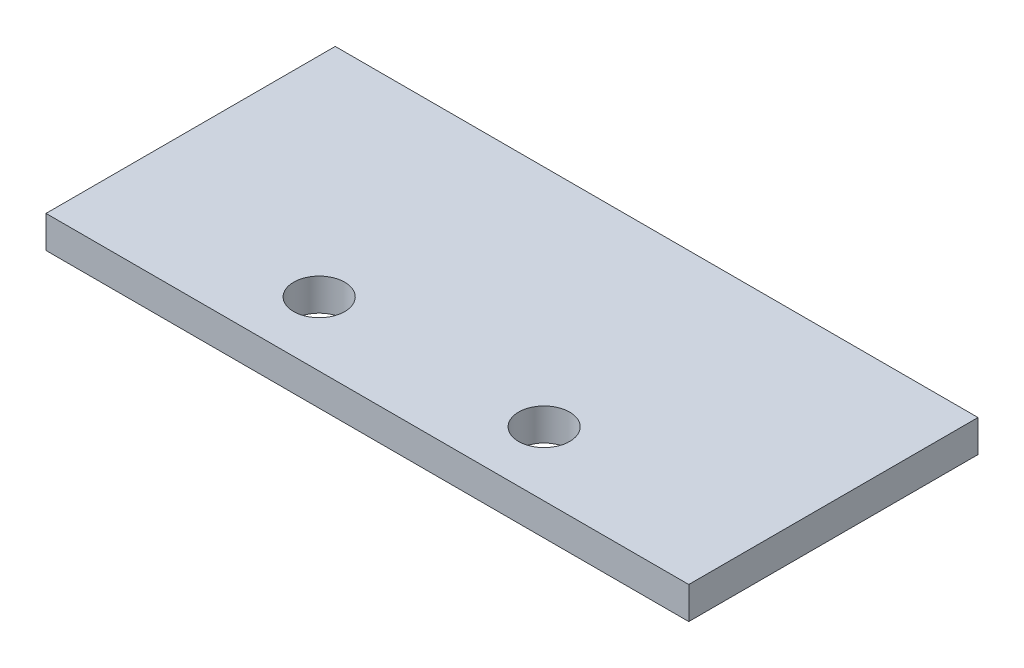
SolidWorks part; units mm, degrees
material "6061-T6 (SS)"
ref_plane "Front Plane" through (0, 0, 0) normal (0, 0, 1) x (1, 0, 0)
ref_plane "Top Plane" through (0, 0, 0) normal (0, 1, 0) x (1, 0, 0)
ref_plane "Right Plane" through (0, 0, 0) normal (1, 0, 0) x (0, 0, -1)
sketch "Sketch1" plane through (0, 0, 0) normal (0, 1, 0) x (1, 0, 0)
  line L1 (0, 0) -> (127, 0)
  line L2 (0, 0) -> (0, 57.15)
  line L3 (0, 57.15) -> (127, 57.15)
  line L4 (127, 0) -> (127, 57.15)
  dimension "D1" = 57.15
  dimension "D2" = 127
extrude "Boss-Extrude1" add sketch "Sketch1" along normal blind 6.35
sketch "Sketch2" plane through (0, 6.35, 0) normal (0, 1, 0) x (1, 0, 0)
  circle A0 centre (41.275, 12.7) radius 5.0419
  circle A1 centre (85.725, 12.7) radius 5.0419
  dimension "D1" = 10.0838
  dimension "D2" = 10.0838
extrude "Cut-Extrude1" cut sketch "Sketch2" against normal through all
